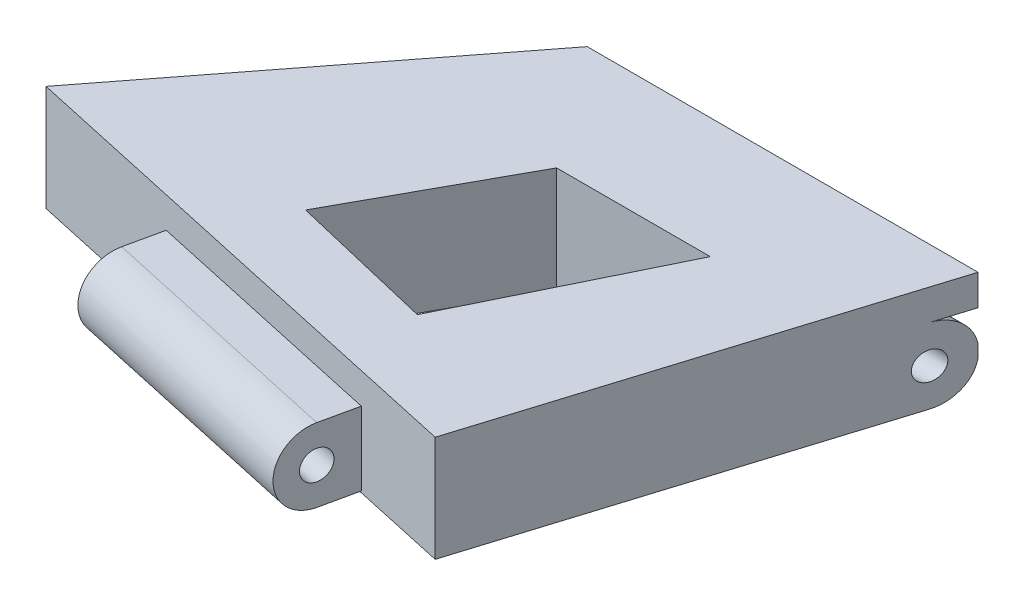
SolidWorks part; units mm, degrees
ref_plane "Front Plane" through (0, 0, 0) normal (0, 0, 1) x (1, 0, 0)
ref_plane "Top Plane" through (0, 0, 0) normal (0, 1, 0) x (1, 0, 0)
ref_plane "Right Plane" through (0, 0, 0) normal (1, 0, 0) x (0, 0, -1)
sketch "Sketch1" plane through (0, 0, 0) normal (0, 1, 0) x (1, 0, 0)
  line L0 (0, 0) -> (19.0568, 0)
  line L1 (19.0568, 0) -> (19.0568, 6.0979)
  line L2 (19.0568, 6.0979) -> (26.174, 6.0979)
  line L3 (26.174, 6.0979) -> (15.5632, -28.0954)
  line L4 (0, 0) -> (0, 6.0979)
  line L5 (0, 6.0979) -> (-6.0827, 6.0979)
  line L6 (-6.0827, 6.0979) -> (-25.5763, -19.0784)
  line L7 (-25.5763, -19.0784) -> (-12.8695, -21.8635)
  line L9 (-12.8695, -21.8635) -> (-14.1912, -27.8936)
  line L10 (-14.1912, -27.8936) -> (6.4307, -32.4136)
  line L11 (6.4307, -32.4136) -> (7.7524, -26.3835)
  line L12 (7.7524, -26.3835) -> (15.5632, -28.0954)
  dimension "D1" = 127.75
  dimension "D2" = 72.76
extrude "Boss-Extrude1" add sketch "Sketch1" along normal blind 15.24
sketch "Sketch2" plane through (0, 15.24, 0) normal (0, 1, 0) x (1, 0, 0)
  line L0 (-12.8695, -21.8635) -> (7.7524, -26.3835)
  line L1 (7.7524, -26.3835) -> (6.4307, -32.4136)
  line L2 (6.4307, -32.4136) -> (-14.1912, -27.8936)
  line L3 (-14.1912, -27.8936) -> (-12.8695, -21.8635)
extrude "Cut-Extrude2" cut sketch "Sketch2" against normal blind 2.54
sketch "Sketch3" plane through (12.9148, 0, 2.8307) normal (0.9768, 0, 0.2141) x (0.2141, 0, -0.9768)
  line L0 (-24.1119, 12.7) -> (-24.1119, 0) construction
  line L1 (-30.2852, 12.7) -> (-24.1119, 12.7)
  line L2 (-30.2852, 12.7) -> (-30.2852, 6.6324)
  line L3 (-30.2852, 6.6324) -> (-24.1119, 6.6324)
  line L4 (-24.1119, 12.7) -> (-24.1119, 6.6324)
  line L5 (-30.2852, 12.7) -> (-24.1119, 6.6324)
  line L7 (-30.2852, 12.7) -> (-24.1119, 12.7)
  line L8 (-30.2852, 12.7) -> (-30.2852, 0)
  line L9 (-30.2852, 0) -> (-24.1119, 0)
  line L10 (-24.1119, 12.7) -> (-24.1119, 0)
  circle A0 centre (-27.1985, 9.6662) radius 3.0338
  circle A1 centre (-27.1985, 9.6662) radius 1.1985
  line M1 (-24.1119, 0) -> (-24.1119, 12.7)
  line M3 (-30.2852, 12.7) -> (-30.2852, 0)
  line M4 (-30.2852, 0) -> (-24.1119, 0)
extrude "Cut-Extrude3" cut sketch "Sketch3" against normal blind 26.416 contours A0 L5 L3 M3 | A0 L7 L5 | L5 A1 | L5 A1 | L3 M3 M4 M1
sketch "Sketch4" plane through (0, 15.24, 0) normal (0, 1, 0) x (1, 0, 0)
  line L0 (0, 0) -> (0, 6.0979)
  line L1 (0, 6.0979) -> (-6.0827, 6.0979)
  line L2 (-6.0827, 6.0979) -> (-10.8042, 0)
  line L3 (-6.0827, 6.0979) -> (-25.5763, -19.0784) construction
  line L4 (-10.8042, 0) -> (0, 0)
  line L5 (19.0568, 0) -> (24.2817, 0)
  line L6 (15.5632, -28.0954) -> (26.174, 6.0979) construction
  line L7 (24.2817, 0) -> (26.174, 6.0979)
  line L8 (26.174, 6.0979) -> (19.0568, 6.0979)
  line L9 (19.0568, 6.0979) -> (19.0568, 0)
extrude "Cut-Extrude4" cut sketch "Sketch4" against normal blind 2.54
sketch "Sketch5" plane through (19.0568, 0, 0) normal (-1, 0, 0) x (0, 0, 1)
  line L0 (-6.0979, 12.7) -> (0, 6.5069)
  line L1 (-6.0979, 12.7) -> (0, 12.7)
  line L2 (-6.0979, 12.7) -> (-6.0979, 6.5069)
  line L3 (-6.0979, 6.5069) -> (0, 6.5069)
  line L4 (0, 12.7) -> (0, 6.5069)
  line L5 (0, 6.5069) -> (0, 0)
  line L6 (0, 0) -> (-6.0979, 0)
  line L7 (-6.0979, 0) -> (-6.0979, 6.5069)
  circle A0 centre (-3.0489, 9.6034) radius 3.0966
  circle A1 centre (-3.0489, 9.6034) radius 1.1487
  line M2 (-6.0979, 12.7) -> (-6.0979, 0)
  line M3 (-6.0979, 0) -> (0, 0)
  line M4 (0, 0) -> (0, 12.7)
extrude "Cut-Extrude5" cut sketch "Sketch5" against normal blind 16.256 and the other way blind 37.592 contours L0 A1 | L0 A1 | A0 L3 M2 | L3 M2 M3 M4 | A0 L0 M2 | A0 L1 L0
sketch "Sketch6" plane through (0, 0, 0) normal (1, 0, 0) x (0, 0, -1)
  line L0 (0, 6.5069) -> (-28.0954, 6.5069)
  line L1 (-28.0954, 15.24) -> (-28.0954, 0) construction
  line L2 (-28.0954, 6.5069) -> (-28.0954, 0)
  line L3 (-28.0954, 0) -> (0, 0)
  line L4 (0, 0) -> (0, 6.5069)
extrude "Cut-Extrude6" cut sketch "Sketch6" against normal blind 30.988 and the other way blind 33.782
sketch "Sketch7" plane through (0, 15.24, 0) normal (0, 1, 0) x (1, 0, 0)
  line L0 (0, 0) -> (19.0568, 0)
  line L1 (-12.8695, -21.8635) -> (7.7524, -26.3835)
  line L2 (9.5284, 0) -> (-2.5586, -24.1235)
  line L3 (7.6073, -3.8342) -> (14.009, -3.8342)
  line L4 (7.6073, -3.8342) -> (1.3205, -3.8342)
  line L5 (1.3205, -3.8342) -> (-6.0289, -17.2022)
  line L6 (14.009, -3.8342) -> (6.0663, -20.0695)
  line L7 (6.0663, -20.0695) -> (-6.0289, -17.2022)
extrude "Cut-Extrude7" cut sketch "Sketch7" against normal blind 30.988 contours L7 L6 L3 L2 | L7 L2 L4 L5
sketch "Sketch8" plane through (0, 15.24, 0) normal (0, 1, 0) x (1, 0, 0)
  line L0 (-10.8042, 0) -> (24.2817, 0)
  line L1 (24.2817, 0) -> (26.174, 6.0979)
  line L2 (26.174, 6.0979) -> (-6.0827, 6.0979)
  line L3 (-6.0827, 6.0979) -> (-10.8042, 0)
extrude "Boss-Extrude2" add sketch "Sketch8" against normal blind 2.54
